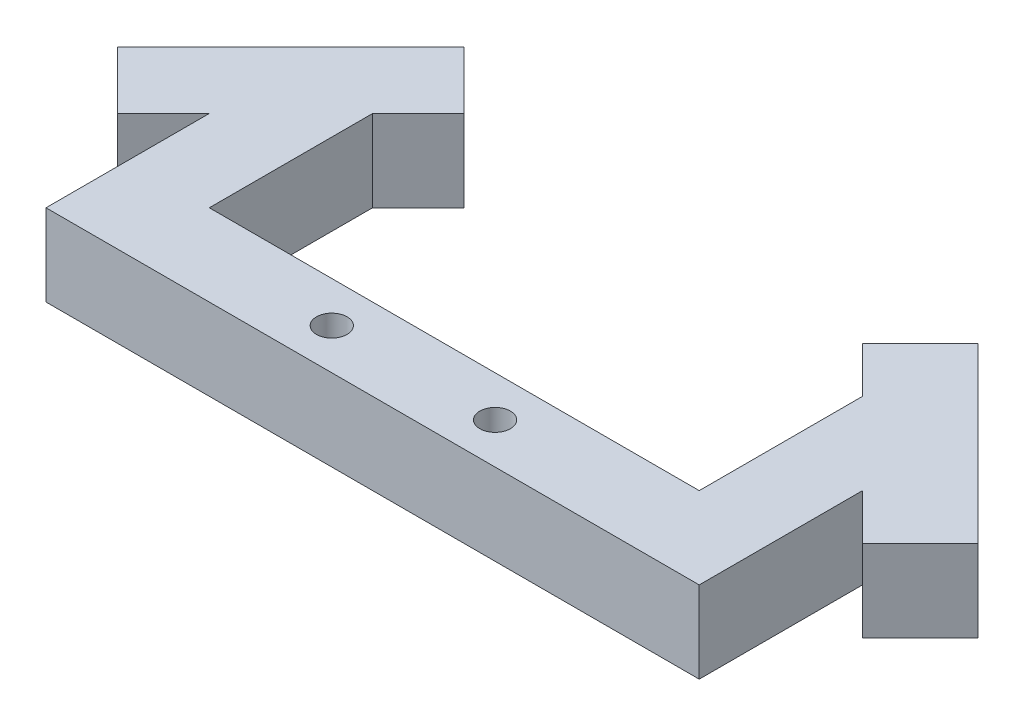
SolidWorks part; units mm, degrees
ref_plane "Front Plane" through (0, 0, 0) normal (0, 0, 1) x (1, 0, 0)
ref_plane "Top Plane" through (0, 0, 0) normal (0, 1, 0) x (1, 0, 0)
ref_plane "Right Plane" through (0, 0, 0) normal (1, 0, 0) x (0, 0, -1)
sketch "Sketch1" plane through (0, 0, 0) normal (0, 1, 0) x (1, 0, 0)
  line L0 (101.6, 0) -> (-101.6, 0)
  line L1 (-101.6, 0) -> (-76.2, 25.4) construction
  line L2 (-76.2, 25.4) -> (76.2, 25.4)
  line L3 (0, 25.4) -> (0, 0) construction
  line L4 (-101.6, 0) -> (-101.6, 50.8)
  line L5 (-101.6, 50.8) -> (-76.2, 76.2)
  line L6 (-76.2, 76.2) -> (-76.2, 25.4)
  line L7 (-101.6, 50.8) -> (-115.8408, 36.5592)
  line L8 (-115.8408, 36.5592) -> (-133.8013, 54.5197)
  line L9 (-133.8013, 54.5197) -> (-79.9197, 108.4013)
  line L10 (-106.8605, 81.4605) -> (-88.9, 63.5) construction
  line L11 (-101.6, 25.4) -> (-76.2, 25.4) construction
  line L12 (-76.2, 76.2) -> (-61.9592, 90.4408)
  line L13 (-61.9592, 90.4408) -> (-79.9197, 108.4013)
  line L14 (101.6, 25.4) -> (76.2, 25.4) construction
  line L15 (106.8605, 81.4605) -> (88.9, 63.5) construction
  line L16 (101.6, 0) -> (76.2, 25.4) construction
  line L17 (61.9592, 90.4408) -> (79.9197, 108.4013)
  line L18 (76.2, 76.2) -> (61.9592, 90.4408)
  line L19 (133.8013, 54.5197) -> (79.9197, 108.4013)
  line L20 (115.8408, 36.5592) -> (133.8013, 54.5197)
  line L21 (101.6, 50.8) -> (115.8408, 36.5592)
  line L22 (76.2, 76.2) -> (76.2, 25.4)
  line L23 (101.6, 50.8) -> (76.2, 76.2)
  line L24 (101.6, 0) -> (101.6, 50.8)
  point P4 (0, 0)
  point P29 (-72.9327, 133.8353)
  point P30 (-136.81, 50.8)
  dimension "D1" = 101.6
  dimension "D2" = 25.4
  dimension "D3" = 76.2
  dimension "D4" = 45
  dimension "D5" = 76.2
extrude "Boss-Extrude1" add sketch "Sketch1" along normal blind 25.4 contours L0 L24 L23 L22 L2 L6 L5 L4 | L12 L13 L9 L8 L7 L5 | L23 L21 L20 L19 L17 L18
sketch "Sketch2" plane through (0, 25.4, 0) normal (0, 1, 0) x (1, 0, 0)
  line L0 (0, 0) -> (0, 25.4) construction
  line L1 (-76.2, 25.4) -> (76.2, 25.4) construction
  line L2 (-25.4, 12.7) -> (25.4, 12.7) construction
  circle A0 centre (25.4, 12.7) radius 4.7625
  circle A1 centre (-25.4, 12.7) radius 4.7625
  point P8 (0, 12.7)
  dimension "D1" = 9.525
  dimension "D2" = 50.8
extrude "Cut-Extrude1" cut sketch "Sketch2" against normal through all both and the other way through all
